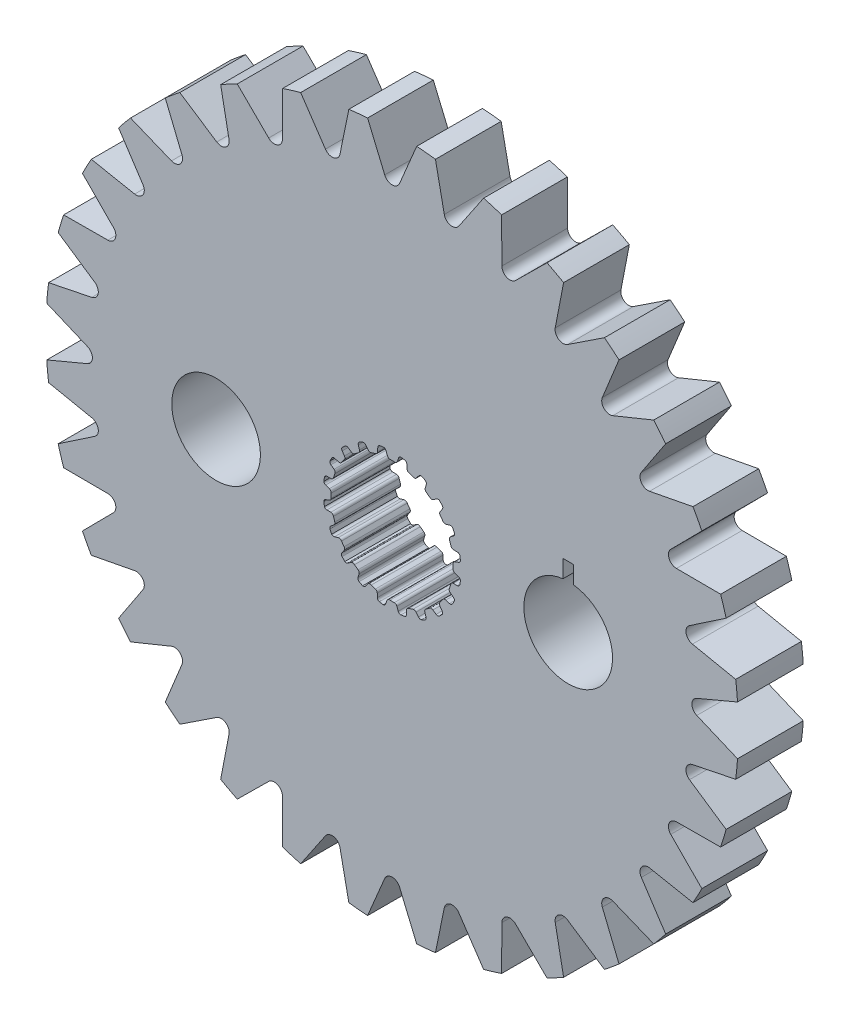
SolidWorks part; units mm, degrees
ref_plane "Front Plane" through (0, 0, 0) normal (0, 0, 1) x (1, 0, 0)
ref_plane "Top Plane" through (0, 0, 0) normal (0, 1, 0) x (1, 0, 0)
ref_plane "Right Plane" through (0, 0, 0) normal (1, 0, 0) x (0, 0, -1)
sketch "Sketch1" plane through (0, 0, 0) normal (0, 0, 1) x (1, 0, 0)
  line L0 (-0.1069, 2.9699) -> (0.1069, 2.9699)
  line L1 (0.3159, 3.2375) -> (0.2537, 3.0575)
  line L2 (-0.2964, 3.2367) -> (-0.2318, 3.0575)
  line L3 (-0.2964, 3.2367) -> (0.3159, 3.2375) construction
  line L4 (0, 3.3252) -> (0, 0) construction
  line L5 (-0.2318, 3.0575) -> (0.2537, 3.0575) construction
  line L6 (-0.4281, 3.3241) -> (0.4281, 3.3263) construction
  line L7 (0.7183, 3.1698) -> (0.7244, 2.9795)
  line L8 (0.816, 2.8576) -> (1.0195, 2.7915)
  line L9 (1.3009, 2.9815) -> (1.1862, 2.8295)
  line L10 (1.6627, 2.7927) -> (1.6097, 2.6099)
  line L11 (1.6591, 2.4655) -> (1.8322, 2.3398)
  line L12 (2.1585, 2.4335) -> (2.0025, 2.3245)
  line L13 (2.4443, 2.1423) -> (2.3374, 1.9847)
  line L14 (2.3398, 1.8322) -> (2.4655, 1.6591)
  line L15 (2.8049, 1.6474) -> (2.6228, 1.5919)
  line L16 (2.9866, 1.2821) -> (2.8363, 1.1653)
  line L17 (2.7915, 1.0195) -> (2.8576, 0.816)
  line L18 (3.1767, 0.7) -> (2.9863, 0.7035)
  line L19 (3.2367, 0.2964) -> (3.0575, 0.2318)
  line L20 (2.9699, 0.1069) -> (2.9699, -0.1069)
  line L21 (3.2375, -0.3159) -> (3.0575, -0.2537)
  line L22 (3.1698, -0.7183) -> (2.9795, -0.7244)
  line L23 (2.8576, -0.816) -> (2.7915, -1.0195)
  line L24 (2.9815, -1.3009) -> (2.8295, -1.1862)
  line L25 (2.7927, -1.6627) -> (2.6099, -1.6097)
  line L26 (2.4655, -1.6591) -> (2.3398, -1.8322)
  line L27 (2.4335, -2.1585) -> (2.3245, -2.0025)
  line L28 (2.1423, -2.4443) -> (1.9847, -2.3374)
  line L29 (1.8322, -2.3398) -> (1.6591, -2.4655)
  line L30 (1.6474, -2.8049) -> (1.5919, -2.6228)
  line L31 (1.2821, -2.9866) -> (1.1653, -2.8363)
  line L32 (1.0195, -2.7915) -> (0.816, -2.8576)
  line L33 (0.7, -3.1767) -> (0.7035, -2.9863)
  line L34 (0.2964, -3.2367) -> (0.2318, -3.0575)
  line L35 (0.1069, -2.9699) -> (-0.1069, -2.9699)
  line L36 (-0.3159, -3.2375) -> (-0.2537, -3.0575)
  line L37 (-0.7183, -3.1698) -> (-0.7244, -2.9795)
  line L38 (-0.816, -2.8576) -> (-1.0195, -2.7915)
  line L39 (-1.3009, -2.9815) -> (-1.1862, -2.8295)
  line L40 (-1.6627, -2.7927) -> (-1.6097, -2.6099)
  line L41 (-1.6591, -2.4655) -> (-1.8322, -2.3398)
  line L42 (-2.1585, -2.4335) -> (-2.0025, -2.3245)
  line L43 (-2.4443, -2.1423) -> (-2.3374, -1.9847)
  line L44 (-2.3398, -1.8322) -> (-2.4655, -1.6591)
  line L45 (-2.8049, -1.6474) -> (-2.6228, -1.5919)
  line L46 (-2.9866, -1.2821) -> (-2.8363, -1.1653)
  line L47 (-2.7915, -1.0195) -> (-2.8576, -0.816)
  line L48 (-3.1767, -0.7) -> (-2.9863, -0.7035)
  line L49 (-3.2367, -0.2964) -> (-3.0575, -0.2318)
  line L50 (-2.9699, -0.1069) -> (-2.9699, 0.1069)
  line L51 (-3.2375, 0.3159) -> (-3.0575, 0.2537)
  line L52 (-3.1698, 0.7183) -> (-2.9795, 0.7244)
  line L53 (-2.8576, 0.816) -> (-2.7915, 1.0195)
  line L54 (-2.9815, 1.3009) -> (-2.8295, 1.1862)
  line L55 (-2.7927, 1.6627) -> (-2.6099, 1.6097)
  line L56 (-2.4655, 1.6591) -> (-2.3398, 1.8322)
  line L57 (-2.4335, 2.1585) -> (-2.3245, 2.0025)
  line L58 (-2.1423, 2.4443) -> (-1.9847, 2.3374)
  line L59 (-1.8322, 2.3398) -> (-1.6591, 2.4655)
  line L60 (-1.6474, 2.8049) -> (-1.5919, 2.6228)
  line L61 (-1.2821, 2.9866) -> (-1.1653, 2.8363)
  line L62 (-1.0195, 2.7915) -> (-0.816, 2.8576)
  line L63 (-0.7, 3.1767) -> (-0.7035, 2.9863)
  line L64 (0.4281, 3.3263) -> (0.62, 3.2938)
  line L65 (1.4351, 3.0312) -> (1.6075, 2.9409)
  line L66 (2.3015, 2.4394) -> (2.4376, 2.3003)
  line L67 (2.9427, 1.6088) -> (3.0291, 1.4344)
  line L68 (3.2958, 0.6207) -> (3.3241, 0.4281)
  line L69 (3.3263, -0.4281) -> (3.2938, -0.62)
  line L70 (3.0312, -1.4351) -> (2.9409, -1.6075)
  line L71 (2.4394, -2.3015) -> (2.3003, -2.4376)
  line L72 (1.6088, -2.9427) -> (1.4344, -3.0291)
  line L73 (0.6207, -3.2958) -> (0.4281, -3.3241)
  line L74 (-0.4281, -3.3263) -> (-0.62, -3.2938)
  line L75 (-1.4351, -3.0312) -> (-1.6075, -2.9409)
  line L76 (-2.3015, -2.4394) -> (-2.4376, -2.3003)
  line L77 (-2.9427, -1.6088) -> (-3.0291, -1.4344)
  line L78 (-3.2958, -0.6207) -> (-3.3241, -0.4281)
  line L79 (-3.3263, 0.4281) -> (-3.2938, 0.62)
  line L80 (-3.0312, 1.4351) -> (-2.9409, 1.6075)
  line L81 (-2.4394, 2.3015) -> (-2.3003, 2.4376)
  line L82 (-1.6088, 2.9427) -> (-1.4344, 3.0291)
  line L83 (-0.6207, 3.2958) -> (-0.4281, 3.3241)
  arc A0 (0.2537, 3.0575) -> (0.1069, 2.9699) centre (0.1283, 3.1009) cw
  arc A1 (-0.2318, 3.0575) -> (-0.1069, 2.9699) centre (-0.1069, 3.1026) ccw
  arc A2 (0.62, 3.2938) -> (0.7183, 3.1698) centre (0.5856, 3.1656) cw
  arc A3 (0.7244, 2.9795) -> (0.816, 2.8576) centre (0.857, 2.9838) ccw
  arc A4 (-0.4281, 3.3241) -> (-0.2964, 3.2367) centre (-0.4213, 3.1916) cw
  arc A5 (0.4281, 3.3263) -> (0.3159, 3.2375) centre (0.4413, 3.1942) ccw
  arc A6 (1.1862, 2.8295) -> (1.0195, 2.7915) centre (1.0802, 2.9095) cw
  arc A7 (1.4351, 3.0312) -> (1.3009, 2.9815) centre (1.4068, 2.9015) ccw
  arc A8 (1.6075, 2.9409) -> (1.6627, 2.7927) centre (1.5352, 2.8297) cw
  arc A9 (1.6097, 2.6099) -> (1.6591, 2.4655) centre (1.7371, 2.5729) ccw
  arc A10 (2.0025, 2.3245) -> (1.8322, 2.3398) centre (1.9264, 2.4332) cw
  arc A11 (2.3015, 2.4394) -> (2.1585, 2.4335) centre (2.2346, 2.3248) ccw
  arc A12 (2.4376, 2.3003) -> (2.4443, 2.1423) centre (2.3345, 2.2168) cw
  arc A13 (2.3374, 1.9847) -> (2.3398, 1.8322) centre (2.4472, 1.9102) ccw
  arc A14 (2.6228, 1.5919) -> (2.4655, 1.6591) centre (2.5841, 1.7189) cw
  arc A15 (2.9427, 1.6088) -> (2.8049, 1.6474) centre (2.8436, 1.5205) ccw
  arc A16 (3.0291, 1.4344) -> (2.9866, 1.2821) centre (2.9052, 1.3869) cw
  arc A17 (2.8363, 1.1653) -> (2.7915, 1.0195) centre (2.9177, 1.0605) ccw
  arc A18 (2.9863, 0.7035) -> (2.8576, 0.816) centre (2.9887, 0.8362) cw
  arc A19 (3.2958, 0.6207) -> (3.1767, 0.7) centre (3.1743, 0.5673) ccw
  arc A20 (3.3241, 0.4281) -> (3.2367, 0.2964) centre (3.1916, 0.4213) cw
  arc A21 (3.0575, 0.2318) -> (2.9699, 0.1069) centre (3.1026, 0.1069) ccw
  arc A22 (3.0575, -0.2537) -> (2.9699, -0.1069) centre (3.1009, -0.1283) cw
  arc A23 (3.3263, -0.4281) -> (3.2375, -0.3159) centre (3.1942, -0.4413) ccw
  arc A24 (3.2938, -0.62) -> (3.1698, -0.7183) centre (3.1656, -0.5856) cw
  arc A25 (2.9795, -0.7244) -> (2.8576, -0.816) centre (2.9838, -0.857) ccw
  arc A26 (2.8295, -1.1862) -> (2.7915, -1.0195) centre (2.9095, -1.0802) cw
  arc A27 (3.0312, -1.4351) -> (2.9815, -1.3009) centre (2.9015, -1.4068) ccw
  arc A28 (2.9409, -1.6075) -> (2.7927, -1.6627) centre (2.8297, -1.5352) cw
  arc A29 (2.6099, -1.6097) -> (2.4655, -1.6591) centre (2.5729, -1.7371) ccw
  arc A30 (2.3245, -2.0025) -> (2.3398, -1.8322) centre (2.4332, -1.9264) cw
  arc A31 (2.4394, -2.3015) -> (2.4335, -2.1585) centre (2.3248, -2.2346) ccw
  arc A32 (2.3003, -2.4376) -> (2.1423, -2.4443) centre (2.2168, -2.3345) cw
  arc A33 (1.9847, -2.3374) -> (1.8322, -2.3398) centre (1.9102, -2.4472) ccw
  arc A34 (1.5919, -2.6228) -> (1.6591, -2.4655) centre (1.7189, -2.5841) cw
  arc A35 (1.6088, -2.9427) -> (1.6474, -2.8049) centre (1.5205, -2.8436) ccw
  arc A36 (1.4344, -3.0291) -> (1.2821, -2.9866) centre (1.3869, -2.9052) cw
  arc A37 (1.1653, -2.8363) -> (1.0195, -2.7915) centre (1.0605, -2.9177) ccw
  arc A38 (0.7035, -2.9863) -> (0.816, -2.8576) centre (0.8362, -2.9887) cw
  arc A39 (0.6207, -3.2958) -> (0.7, -3.1767) centre (0.5673, -3.1743) ccw
  arc A40 (0.4281, -3.3241) -> (0.2964, -3.2367) centre (0.4213, -3.1916) cw
  arc A41 (0.2318, -3.0575) -> (0.1069, -2.9699) centre (0.1069, -3.1026) ccw
  arc A42 (-0.2537, -3.0575) -> (-0.1069, -2.9699) centre (-0.1283, -3.1009) cw
  arc A43 (-0.4281, -3.3263) -> (-0.3159, -3.2375) centre (-0.4413, -3.1942) ccw
  arc A44 (-0.62, -3.2938) -> (-0.7183, -3.1698) centre (-0.5856, -3.1656) cw
  arc A45 (-0.7244, -2.9795) -> (-0.816, -2.8576) centre (-0.857, -2.9838) ccw
  arc A46 (-1.1862, -2.8295) -> (-1.0195, -2.7915) centre (-1.0802, -2.9095) cw
  arc A47 (-1.4351, -3.0312) -> (-1.3009, -2.9815) centre (-1.4068, -2.9015) ccw
  arc A48 (-1.6075, -2.9409) -> (-1.6627, -2.7927) centre (-1.5352, -2.8297) cw
  arc A49 (-1.6097, -2.6099) -> (-1.6591, -2.4655) centre (-1.7371, -2.5729) ccw
  arc A50 (-2.0025, -2.3245) -> (-1.8322, -2.3398) centre (-1.9264, -2.4332) cw
  arc A51 (-2.3015, -2.4394) -> (-2.1585, -2.4335) centre (-2.2346, -2.3248) ccw
  arc A52 (-2.4376, -2.3003) -> (-2.4443, -2.1423) centre (-2.3345, -2.2168) cw
  arc A53 (-2.3374, -1.9847) -> (-2.3398, -1.8322) centre (-2.4472, -1.9102) ccw
  arc A54 (-2.6228, -1.5919) -> (-2.4655, -1.6591) centre (-2.5841, -1.7189) cw
  arc A55 (-2.9427, -1.6088) -> (-2.8049, -1.6474) centre (-2.8436, -1.5205) ccw
  arc A56 (-3.0291, -1.4344) -> (-2.9866, -1.2821) centre (-2.9052, -1.3869) cw
  arc A57 (-2.8363, -1.1653) -> (-2.7915, -1.0195) centre (-2.9177, -1.0605) ccw
  arc A58 (-2.9863, -0.7035) -> (-2.8576, -0.816) centre (-2.9887, -0.8362) cw
  arc A59 (-3.2958, -0.6207) -> (-3.1767, -0.7) centre (-3.1743, -0.5673) ccw
  arc A60 (-3.3241, -0.4281) -> (-3.2367, -0.2964) centre (-3.1916, -0.4213) cw
  arc A61 (-3.0575, -0.2318) -> (-2.9699, -0.1069) centre (-3.1026, -0.1069) ccw
  arc A62 (-3.0575, 0.2537) -> (-2.9699, 0.1069) centre (-3.1009, 0.1283) cw
  arc A63 (-3.3263, 0.4281) -> (-3.2375, 0.3159) centre (-3.1942, 0.4413) ccw
  arc A64 (-3.2938, 0.62) -> (-3.1698, 0.7183) centre (-3.1656, 0.5856) cw
  arc A65 (-2.9795, 0.7244) -> (-2.8576, 0.816) centre (-2.9838, 0.857) ccw
  arc A66 (-2.8295, 1.1862) -> (-2.7915, 1.0195) centre (-2.9095, 1.0802) cw
  arc A67 (-3.0312, 1.4351) -> (-2.9815, 1.3009) centre (-2.9015, 1.4068) ccw
  arc A68 (-2.9409, 1.6075) -> (-2.7927, 1.6627) centre (-2.8297, 1.5352) cw
  arc A69 (-2.6099, 1.6097) -> (-2.4655, 1.6591) centre (-2.5729, 1.7371) ccw
  arc A70 (-2.3245, 2.0025) -> (-2.3398, 1.8322) centre (-2.4332, 1.9264) cw
  arc A71 (-2.4394, 2.3015) -> (-2.4335, 2.1585) centre (-2.3248, 2.2346) ccw
  arc A72 (-2.3003, 2.4376) -> (-2.1423, 2.4443) centre (-2.2168, 2.3345) cw
  arc A73 (-1.9847, 2.3374) -> (-1.8322, 2.3398) centre (-1.9102, 2.4472) ccw
  arc A74 (-1.5919, 2.6228) -> (-1.6591, 2.4655) centre (-1.7189, 2.5841) cw
  arc A75 (-1.6088, 2.9427) -> (-1.6474, 2.8049) centre (-1.5205, 2.8436) ccw
  arc A76 (-1.4344, 3.0291) -> (-1.2821, 2.9866) centre (-1.3869, 2.9052) cw
  arc A77 (-1.1653, 2.8363) -> (-1.0195, 2.7915) centre (-1.0605, 2.9177) ccw
  arc A78 (-0.7035, 2.9863) -> (-0.816, 2.8576) centre (-0.8362, 2.9887) cw
  arc A79 (-0.6207, 3.2958) -> (-0.7, 3.1767) centre (-0.5673, 3.1743) ccw
  circle A80 centre (0, 0) radius 16.8606
  point P14 (0, 2.9699)
  point P247 (0, 0)
  dimension "D4" = 0.1327
  dimension "D8" = 20
  dimension "D9" = 33.7212
  dimension "D1" = 2.9699
  dimension "D2" = 0.2139
  dimension "D3" = 0.1904
  dimension "D5" = 0.0877
  dimension "D6" = 0.4855
  dimension "D7" = 0.8563
extrude "Boss-Extrude1" add sketch "Sketch1" along normal mid plane 3.2004
sketch "Sketch2" plane through (0, 0, 1.6002) normal (0, 0, 1) x (1, 0, 0)
  line L0 (0, 16.8181) -> (0, 0) construction
  line L1 (1.557, 31.6527) -> (0, 0) construction
  line L2 (-1.1958, 16.8181) -> (1.1958, 16.8181) construction
  line L3 (-0.7785, 15.8263) -> (0.7785, 15.8263) construction
  line L4 (-1.1958, 16.8181) -> (-0.3613, 14.8345)
  line L5 (1.1958, 16.8181) -> (0.3613, 14.8345)
  line L6 (4.4538, 16.2617) -> (3.2484, 14.479)
  line L7 (2.1083, 16.7283) -> (2.5398, 14.62)
  line L8 (7.5408, 15.0803) -> (6.0107, 13.5671)
  line L9 (5.3313, 15.9955) -> (5.3432, 13.8436)
  line L10 (10.3379, 13.3195) -> (8.542, 12.1338)
  line L11 (8.3494, 14.6481) -> (7.9413, 12.5352)
  line L12 (12.7378, 11.0467) -> (10.7451, 10.2342)
  line L13 (11.0467, 12.7378) -> (10.2342, 10.7451)
  line L14 (14.6481, 8.3494) -> (12.5352, 7.9413)
  line L15 (13.3195, 10.3379) -> (12.1338, 8.542)
  line L16 (15.9955, 5.3313) -> (13.8436, 5.3432)
  line L17 (15.0803, 7.5408) -> (13.5671, 6.0107)
  line L18 (16.7283, 2.1083) -> (14.62, 2.5398)
  line L19 (16.2617, 4.4538) -> (14.479, 3.2484)
  line L20 (16.8181, -1.1958) -> (14.8345, -0.3613)
  line L21 (16.8181, 1.1958) -> (14.8345, 0.3613)
  line L22 (16.2617, -4.4538) -> (14.479, -3.2484)
  line L23 (16.7283, -2.1083) -> (14.62, -2.5398)
  line L24 (15.0803, -7.5408) -> (13.5671, -6.0107)
  line L25 (15.9955, -5.3313) -> (13.8436, -5.3432)
  line L26 (13.3195, -10.3379) -> (12.1338, -8.542)
  line L27 (14.6481, -8.3494) -> (12.5352, -7.9413)
  line L28 (11.0467, -12.7378) -> (10.2342, -10.7451)
  line L29 (12.7378, -11.0467) -> (10.7451, -10.2342)
  line L30 (8.3494, -14.6481) -> (7.9413, -12.5352)
  line L31 (10.3379, -13.3195) -> (8.542, -12.1338)
  line L32 (5.3313, -15.9955) -> (5.3432, -13.8436)
  line L33 (7.5408, -15.0803) -> (6.0107, -13.5671)
  line L34 (2.1083, -16.7283) -> (2.5398, -14.62)
  line L35 (4.4538, -16.2617) -> (3.2484, -14.479)
  line L36 (-1.1958, -16.8181) -> (-0.3613, -14.8345)
  line L37 (1.1958, -16.8181) -> (0.3613, -14.8345)
  line L38 (-4.4538, -16.2617) -> (-3.2484, -14.479)
  line L39 (-2.1083, -16.7283) -> (-2.5398, -14.62)
  line L40 (-7.5408, -15.0803) -> (-6.0107, -13.5671)
  line L41 (-5.3313, -15.9955) -> (-5.3432, -13.8436)
  line L42 (-10.3379, -13.3195) -> (-8.542, -12.1338)
  line L43 (-8.3494, -14.6481) -> (-7.9413, -12.5352)
  line L44 (-12.7378, -11.0467) -> (-10.7451, -10.2342)
  line L45 (-11.0467, -12.7378) -> (-10.2342, -10.7451)
  line L46 (-14.6481, -8.3494) -> (-12.5352, -7.9413)
  line L47 (-13.3195, -10.3379) -> (-12.1338, -8.542)
  line L48 (-15.9955, -5.3313) -> (-13.8436, -5.3432)
  line L49 (-15.0803, -7.5408) -> (-13.5671, -6.0107)
  line L50 (-16.7283, -2.1083) -> (-14.62, -2.5398)
  line L51 (-16.2617, -4.4538) -> (-14.479, -3.2484)
  line L52 (-16.8181, 1.1958) -> (-14.8345, 0.3613)
  line L53 (-16.8181, -1.1958) -> (-14.8345, -0.3613)
  line L54 (-16.2617, 4.4538) -> (-14.479, 3.2484)
  line L55 (-16.7283, 2.1083) -> (-14.62, 2.5398)
  line L56 (-15.0803, 7.5408) -> (-13.5671, 6.0107)
  line L57 (-15.9955, 5.3313) -> (-13.8436, 5.3432)
  line L58 (-13.3195, 10.3379) -> (-12.1338, 8.542)
  line L59 (-14.6481, 8.3494) -> (-12.5352, 7.9413)
  line L60 (-11.0467, 12.7378) -> (-10.2342, 10.7451)
  line L61 (-12.7378, 11.0467) -> (-10.7451, 10.2342)
  line L62 (-8.3494, 14.6481) -> (-7.9413, 12.5352)
  line L63 (-10.3379, 13.3195) -> (-8.542, 12.1338)
  line L64 (-5.3313, 15.9955) -> (-5.3432, 13.8436)
  line L65 (-7.5408, 15.0803) -> (-6.0107, 13.5671)
  line L66 (-2.1083, 16.7283) -> (-2.5398, 14.62)
  line L67 (-4.4538, 16.2617) -> (-3.2484, 14.479)
  circle A0 centre (0, 0) radius 16.8606 construction
  arc A1 (-0.3613, 14.8345) -> (0.3613, 14.8345) centre (0, 14.9865) ccw
  arc A2 (-1.1958, 16.8181) -> (1.1958, 16.8181) centre (0, 0) cw
  arc A3 (2.1083, 16.7283) -> (4.4538, 16.2617) centre (0, 0) cw
  arc A4 (2.5398, 14.62) -> (3.2484, 14.479) centre (2.9237, 14.6986) ccw
  arc A5 (5.3313, 15.9955) -> (7.5408, 15.0803) centre (0, 0) cw
  arc A6 (5.3432, 13.8436) -> (6.0107, 13.5671) centre (5.7351, 13.8457) ccw
  arc A7 (8.3494, 14.6481) -> (10.3379, 13.3195) centre (0, 0) cw
  arc A8 (7.9413, 12.5352) -> (8.542, 12.1338) centre (8.3261, 12.4608) ccw
  arc A9 (11.0467, 12.7378) -> (12.7378, 11.0467) centre (0, 0) cw
  arc A10 (10.2342, 10.7451) -> (10.7451, 10.2342) centre (10.5971, 10.5971) ccw
  arc A11 (13.3195, 10.3379) -> (14.6481, 8.3494) centre (0, 0) cw
  arc A12 (12.1338, 8.542) -> (12.5352, 7.9413) centre (12.4608, 8.3261) ccw
  arc A13 (15.0803, 7.5408) -> (15.9955, 5.3313) centre (0, 0) cw
  arc A14 (13.5671, 6.0107) -> (13.8436, 5.3432) centre (13.8457, 5.7351) ccw
  arc A15 (16.2617, 4.4538) -> (16.7283, 2.1083) centre (0, 0) cw
  arc A16 (14.479, 3.2484) -> (14.62, 2.5398) centre (14.6986, 2.9237) ccw
  arc A17 (16.8181, 1.1958) -> (16.8181, -1.1958) centre (0, 0) cw
  arc A18 (14.8345, 0.3613) -> (14.8345, -0.3613) centre (14.9865, 0) ccw
  arc A19 (16.7283, -2.1083) -> (16.2617, -4.4538) centre (0, 0) cw
  arc A20 (14.62, -2.5398) -> (14.479, -3.2484) centre (14.6986, -2.9237) ccw
  arc A21 (15.9955, -5.3313) -> (15.0803, -7.5408) centre (0, 0) cw
  arc A22 (13.8436, -5.3432) -> (13.5671, -6.0107) centre (13.8457, -5.7351) ccw
  arc A23 (14.6481, -8.3494) -> (13.3195, -10.3379) centre (0, 0) cw
  arc A24 (12.5352, -7.9413) -> (12.1338, -8.542) centre (12.4608, -8.3261) ccw
  arc A25 (12.7378, -11.0467) -> (11.0467, -12.7378) centre (0, 0) cw
  arc A26 (10.7451, -10.2342) -> (10.2342, -10.7451) centre (10.5971, -10.5971) ccw
  arc A27 (10.3379, -13.3195) -> (8.3494, -14.6481) centre (0, 0) cw
  arc A28 (8.542, -12.1338) -> (7.9413, -12.5352) centre (8.3261, -12.4608) ccw
  arc A29 (7.5408, -15.0803) -> (5.3313, -15.9955) centre (0, 0) cw
  arc A30 (6.0107, -13.5671) -> (5.3432, -13.8436) centre (5.7351, -13.8457) ccw
  arc A31 (4.4538, -16.2617) -> (2.1083, -16.7283) centre (0, 0) cw
  arc A32 (3.2484, -14.479) -> (2.5398, -14.62) centre (2.9237, -14.6986) ccw
  arc A33 (1.1958, -16.8181) -> (-1.1958, -16.8181) centre (0, 0) cw
  arc A34 (0.3613, -14.8345) -> (-0.3613, -14.8345) centre (0, -14.9865) ccw
  arc A35 (-2.1083, -16.7283) -> (-4.4538, -16.2617) centre (0, 0) cw
  arc A36 (-2.5398, -14.62) -> (-3.2484, -14.479) centre (-2.9237, -14.6986) ccw
  arc A37 (-5.3313, -15.9955) -> (-7.5408, -15.0803) centre (0, 0) cw
  arc A38 (-5.3432, -13.8436) -> (-6.0107, -13.5671) centre (-5.7351, -13.8457) ccw
  arc A39 (-8.3494, -14.6481) -> (-10.3379, -13.3195) centre (0, 0) cw
  arc A40 (-7.9413, -12.5352) -> (-8.542, -12.1338) centre (-8.3261, -12.4608) ccw
  arc A41 (-11.0467, -12.7378) -> (-12.7378, -11.0467) centre (0, 0) cw
  arc A42 (-10.2342, -10.7451) -> (-10.7451, -10.2342) centre (-10.5971, -10.5971) ccw
  arc A43 (-13.3195, -10.3379) -> (-14.6481, -8.3494) centre (0, 0) cw
  arc A44 (-12.1338, -8.542) -> (-12.5352, -7.9413) centre (-12.4608, -8.3261) ccw
  arc A45 (-15.0803, -7.5408) -> (-15.9955, -5.3313) centre (0, 0) cw
  arc A46 (-13.5671, -6.0107) -> (-13.8436, -5.3432) centre (-13.8457, -5.7351) ccw
  arc A47 (-16.2617, -4.4538) -> (-16.7283, -2.1083) centre (0, 0) cw
  arc A48 (-14.479, -3.2484) -> (-14.62, -2.5398) centre (-14.6986, -2.9237) ccw
  arc A49 (-16.8181, -1.1958) -> (-16.8181, 1.1958) centre (0, 0) cw
  arc A50 (-14.8345, -0.3613) -> (-14.8345, 0.3613) centre (-14.9865, 0) ccw
  arc A51 (-16.7283, 2.1083) -> (-16.2617, 4.4538) centre (0, 0) cw
  arc A52 (-14.62, 2.5398) -> (-14.479, 3.2484) centre (-14.6986, 2.9237) ccw
  arc A53 (-15.9955, 5.3313) -> (-15.0803, 7.5408) centre (0, 0) cw
  arc A54 (-13.8436, 5.3432) -> (-13.5671, 6.0107) centre (-13.8457, 5.7351) ccw
  arc A55 (-14.6481, 8.3494) -> (-13.3195, 10.3379) centre (0, 0) cw
  arc A56 (-12.5352, 7.9413) -> (-12.1338, 8.542) centre (-12.4608, 8.3261) ccw
  arc A57 (-12.7378, 11.0467) -> (-11.0467, 12.7378) centre (0, 0) cw
  arc A58 (-10.7451, 10.2342) -> (-10.2342, 10.7451) centre (-10.5971, 10.5971) ccw
  arc A59 (-10.3379, 13.3195) -> (-8.3494, 14.6481) centre (0, 0) cw
  arc A60 (-8.542, 12.1338) -> (-7.9413, 12.5352) centre (-8.3261, 12.4608) ccw
  arc A61 (-7.5408, 15.0803) -> (-5.3313, 15.9955) centre (0, 0) cw
  arc A62 (-6.0107, 13.5671) -> (-5.3432, 13.8436) centre (-5.7351, 13.8457) ccw
  arc A63 (-4.4538, 16.2617) -> (-2.1083, 16.7283) centre (0, 0) cw
  arc A64 (-3.2484, 14.479) -> (-2.5398, 14.62) centre (-2.9237, 14.6986) ccw
  point P9 (0, 15.8263)
  point P171 (0, 0)
  dimension "D1" = 0.9918
  dimension "D2" = 1.557
  dimension "D3" = 20
  dimension "D4" = 32
extrude "Cut-Extrude1" cut sketch "Sketch2" against normal up to surface (3.2004 mm away) up to face at (16.8606, 0, -1.6002)
sketch "Sketch3" plane through (0, 0, 1.6002) normal (0, 0, 1) x (1, 0, 0)
  circle A0 centre (0, 0) radius 15.8688 construction
  circle A1 centre (0, 0) radius 16.8606 construction
  dimension "D1" = 31.7376
sketch "Sketch4" plane through (0, 0, 1.6002) normal (0, 0, 1) x (1, 0, 0)
  line L0 (-8.5725, 0) -> (8.5725, 0) construction
  line L1 (0, 16.8181) -> (0, 0) construction
  circle A0 centre (8.5725, 0) radius 2.159
  circle A1 centre (-8.5725, 0) radius 2.159
  dimension "D1" = 4.318
  dimension "D2" = 17.145
extrude "Cut-Extrude2" cut sketch "Sketch4" against normal up to surface (3.2004 mm away) up to face at (0, 0, -1.6002)
sketch "Sketch5" plane through (0, 0, 1.6002) normal (0, 0, 1) x (1, 0, 0)
  line L0 (8.5725, 1.7323) -> (8.5725, 0) construction
  line L1 (8.8265, 3.0023) -> (8.3185, 3.0023)
  line L2 (8.8265, 3.0023) -> (8.8265, 1.7323)
  line L3 (8.8265, 1.7323) -> (8.3185, 1.7323)
  line L4 (8.3185, 3.0023) -> (8.3185, 1.7323)
  circle A0 centre (8.5725, 0) radius 2.159 construction
  point P8 (8.2173, 1.7322)
  dimension "D1" = 1.27
  dimension "D2" = 0.508
  dimension "D3" = 1.7323
extrude "Cut-Extrude3" cut sketch "Sketch5" against normal up to surface (3.2004 mm away) up to face at (10.7315, 0, -1.6002)
